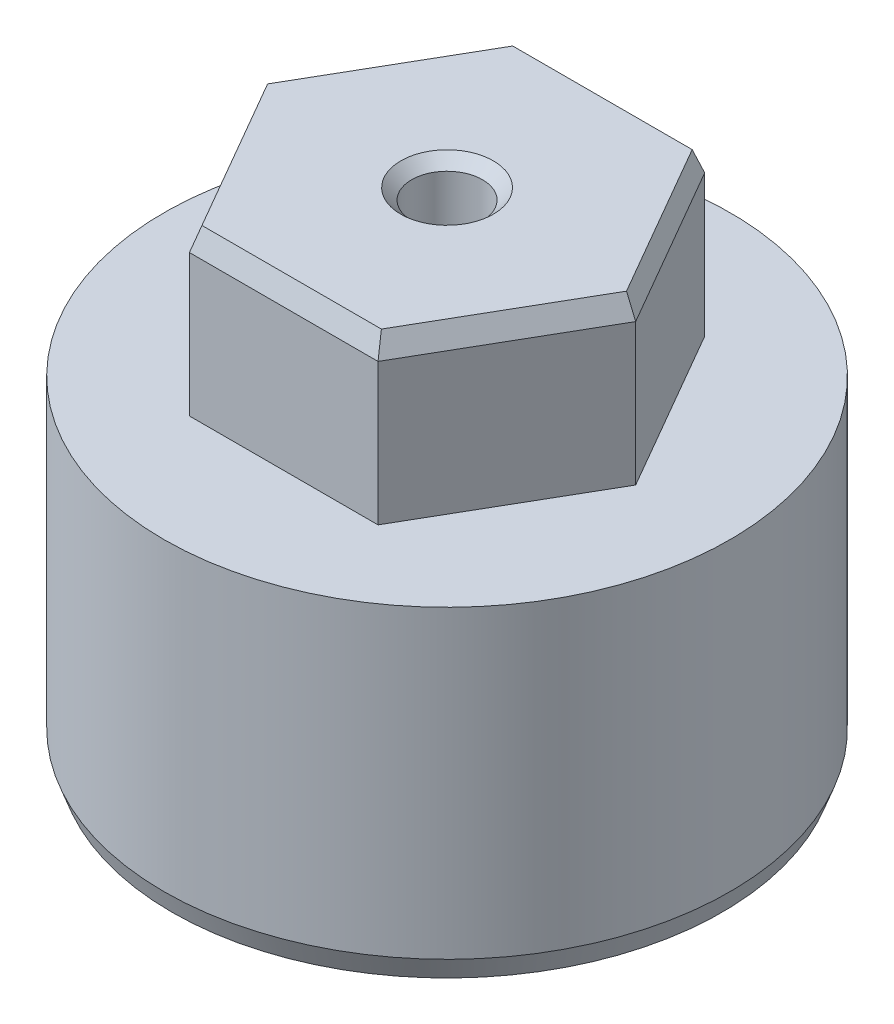
SolidWorks part; units mm, degrees
ref_plane "Front Plane" through (0, 0, 0) normal (0, 0, 1) x (1, 0, 0)
ref_plane "Top Plane" through (0, 0, 0) normal (0, 1, 0) x (1, 0, 0)
ref_plane "Right Plane" through (0, 0, 0) normal (1, 0, 0) x (0, 0, -1)
sketch "Sketch1" plane through (0, 0, 0) normal (0, 1, 0) x (1, 0, 0)
  circle A0 centre (0, 0) radius 26
  dimension "D1" = 52
extrude "Boss-Extrude1" add sketch "Sketch1" along normal mid plane 30
sketch "Sketch2" plane through (0, 15, 0) normal (0, 1, 0) x (1, 0, 0)
  line L1 (-17.3205, 0) -> (-8.6603, -15)
  line L2 (-8.6603, -15) -> (8.6603, -15)
  line L3 (8.6603, -15) -> (17.3205, 0)
  line L4 (17.3205, 0) -> (8.6603, 15)
  line L5 (8.6603, 15) -> (-8.6603, 15)
  line L6 (-8.6603, 15) -> (-17.3205, 0)
  circle A0 centre (0, 0) radius 15 construction
  dimension "D1" = 30
extrude "Boss-Extrude2" add sketch "Sketch2" along normal blind 15
sketch "Sketch3" plane through (0, 30, 0) normal (0, 1, 0) x (1, 0, 0)
  circle A0 centre (0, 0) radius 3.25
  dimension "D1" = 6.5
chamfer "Chamfer1" distance 2 angle 20 6 edges at (-12.9904, 30, -7.5) (-12.9904, 30, 7.5) (0, 30, 15) (12.9904, 30, 7.5) (12.9904, 30, -7.5) (0, 30, -15)
chamfer "Chamfer2" distance 2 angle 20 1 edges at (0, -15, 26)
extrude "Cut-Extrude1" cut sketch "Sketch3" against normal blind 18
chamfer "Chamfer3" distance 1 angle 45 1 edges at (0, 30, 3.25)
